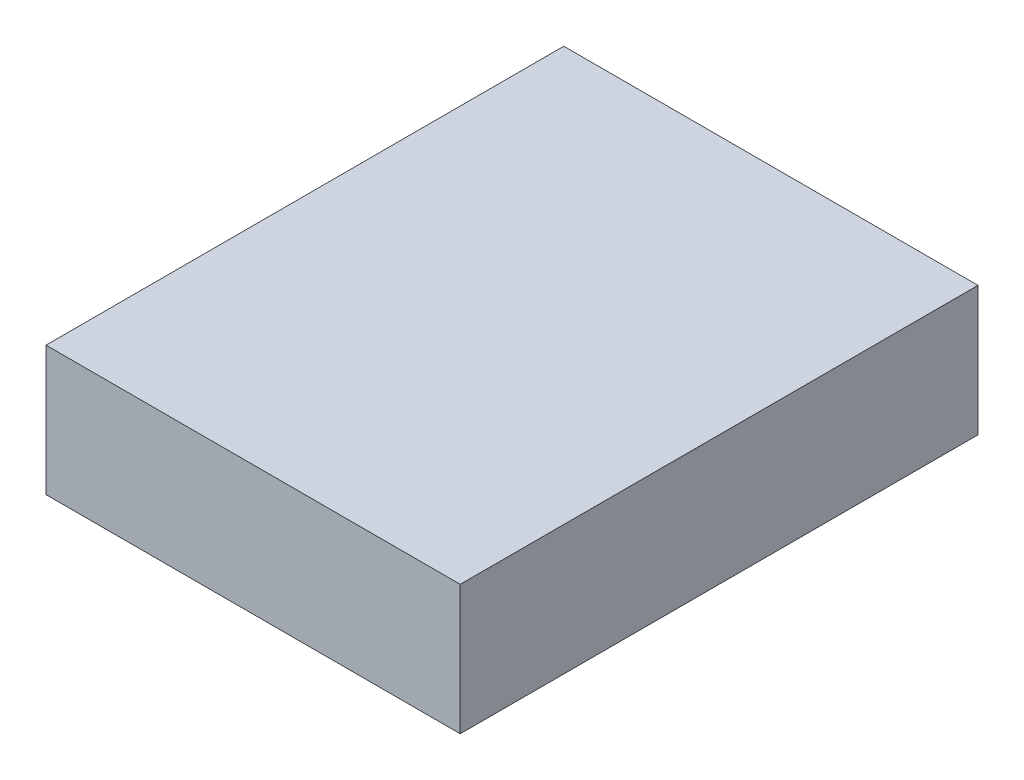
SolidWorks part; units mm, degrees
ref_plane "Front Plane" through (0, 0, 0) normal (0, 0, 1) x (1, 0, 0)
ref_plane "Top Plane" through (0, 0, 0) normal (0, 1, 0) x (1, 0, 0)
ref_plane "Right Plane" through (0, 0, 0) normal (1, 0, 0) x (0, 0, -1)
sketch "Sketch1" plane through (0, 0, 0) normal (0, 0, 1) x (1, 0, 0)
  line L1 (0, 0) -> (406.4, 0)
  line L2 (0, 0) -> (0, 127)
  line L3 (0, 127) -> (406.4, 127)
  line L4 (406.4, 0) -> (406.4, 127)
  dimension "D1" = 406.4
  dimension "D2" = 127
extrude "Boss-Extrude1" add sketch "Sketch1" along normal blind 508
